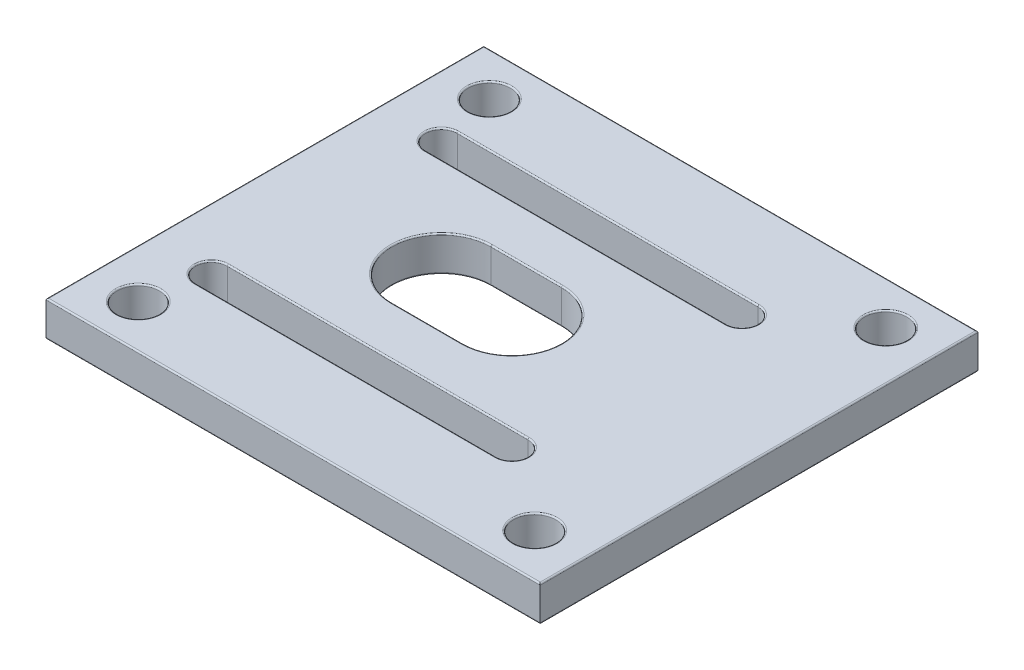
SolidWorks part; units mm, degrees
ref_plane "Front Plane" through (0, 0, 0) normal (0, 0, 1) x (1, 0, 0)
ref_plane "Top Plane" through (0, 0, 0) normal (0, 1, 0) x (1, 0, 0)
ref_plane "Right Plane" through (0, 0, 0) normal (1, 0, 0) x (0, 0, -1)
sketch "Sketch1" plane through (0, 0, 0) normal (0, 1, 0) x (1, 0, 0)
  line L0 (0, 0) -> (-35, 0) construction
  line L5 (-35, 31) -> (35, 31)
  line L6 (-35, 31) -> (-35, -31)
  line L7 (-35, -31) -> (35, -31)
  line L10 (35, 31) -> (35, -31)
  line L13 (0, 0) -> (0, 21) construction
  line L16 (-26.288, 16.288) -> (16.288, 16.288) construction
  line L21 (-26.288, 18.538) -> (16.288, 18.538)
  line L22 (-21, 21) -> (21, 21) construction
  line L27 (-21, 21) -> (-21, -21) construction
  line L28 (-21, -21) -> (21, -21) construction
  line L29 (21, 21) -> (21, -21) construction
  line L30 (-21, 21) -> (21, -21) construction
  line L31 (-21, -21) -> (21, 21) construction
  line L32 (-26.288, 14.038) -> (16.288, 14.038)
  line L33 (-10, 0) -> (0, 0) construction
  line L34 (-10, 7) -> (0, 7)
  line L35 (-10, -7) -> (0, -7)
  line L36 (-26.288, -16.288) -> (16.288, -16.288) construction
  line L37 (-26.288, -18.538) -> (16.288, -18.538)
  line L38 (-26.288, -14.038) -> (16.288, -14.038)
  circle A12 centre (0, 0) radius 37.5 construction
  circle A13 centre (-28.0721, 24.8638) radius 3
  circle A14 centre (28.0721, 24.8638) radius 3
  circle A15 centre (28.0721, -24.8638) radius 3
  circle A16 centre (-28.0721, -24.8638) radius 3
  circle A17 centre (0, 0) radius 23 construction
  circle A18 centre (-16.288, 16.288) radius 2.25 construction
  circle A19 centre (16.288, 16.288) radius 2.25 construction
  arc A20 (-26.288, 18.538) -> (-26.288, 14.038) centre (-26.288, 16.288) ccw
  arc A21 (16.288, 14.038) -> (16.288, 18.538) centre (16.288, 16.288) ccw
  arc A23 (-10, 7) -> (-10, -7) centre (-10, 0) ccw
  arc A24 (0, -7) -> (0, 7) centre (0, 0) ccw
  arc A25 (-26.288, -18.538) -> (-26.288, -14.038) centre (-26.288, -16.288) cw
  arc A26 (16.288, -14.038) -> (16.288, -18.538) centre (16.288, -16.288) cw
  point P0 (0, 0)
  point P27 (-26.288, 16.288)
  point P29 (-5, 16.288)
  point P35 (-10, 0)
  point P37 (-5, 0)
  point P44 (-5, -16.288)
  dimension "D3" = 42
  dimension "D5" = 10
  dimension "D6" = 2.25
  dimension "D7" = 10
  dimension "D8" = 7
  dimension "D1" = 70
  dimension "D2" = 62
  dimension "D4" = 42
extrude "Boss-Extrude2" add sketch "Sketch1" along normal blind 5
fillet "Fillet1" radius 0.2 40 edges at (-5, 0, 14.038) (18.538, 0, 16.288) (-5, 0, 18.538) (-28.538, 0, 16.288) (-5, 0, -18.538) (18.538, 0, -16.288) (-5, 0, -14.038) (-28.538, 0, -16.288) (0, 0, -31) (-35, 0, 0) (0, 0, 31) (35, 0, 0) (-28.0721, 0, -21.8638) (28.0721, 0, -21.8638) (28.0721, 0, 21.8638) (-28.0721, 0, 21.8638) (-5, 0, -7) (7, 0, 0) (-5, 0, 7) (-17, 0, 0) (18.538, 5, 16.288) (-5, 5, 14.038) (-28.538, 5, 16.288) (-5, 5, 18.538) (7, 5, 0) (-5, 5, -7) (-17, 5, 0) (-5, 5, 7) (18.538, 5, -16.288) (-5, 5, -18.538) (-28.538, 5, -16.288) (-5, 5, -14.038) (-28.0721, 5, 21.8638) (28.0721, 5, -21.8638) (0, 5, 31) (-35, 5, 0) (0, 5, -31) (35, 5, 0) (-28.0721, 5, -21.8638) (28.0721, 5, 21.8638)
